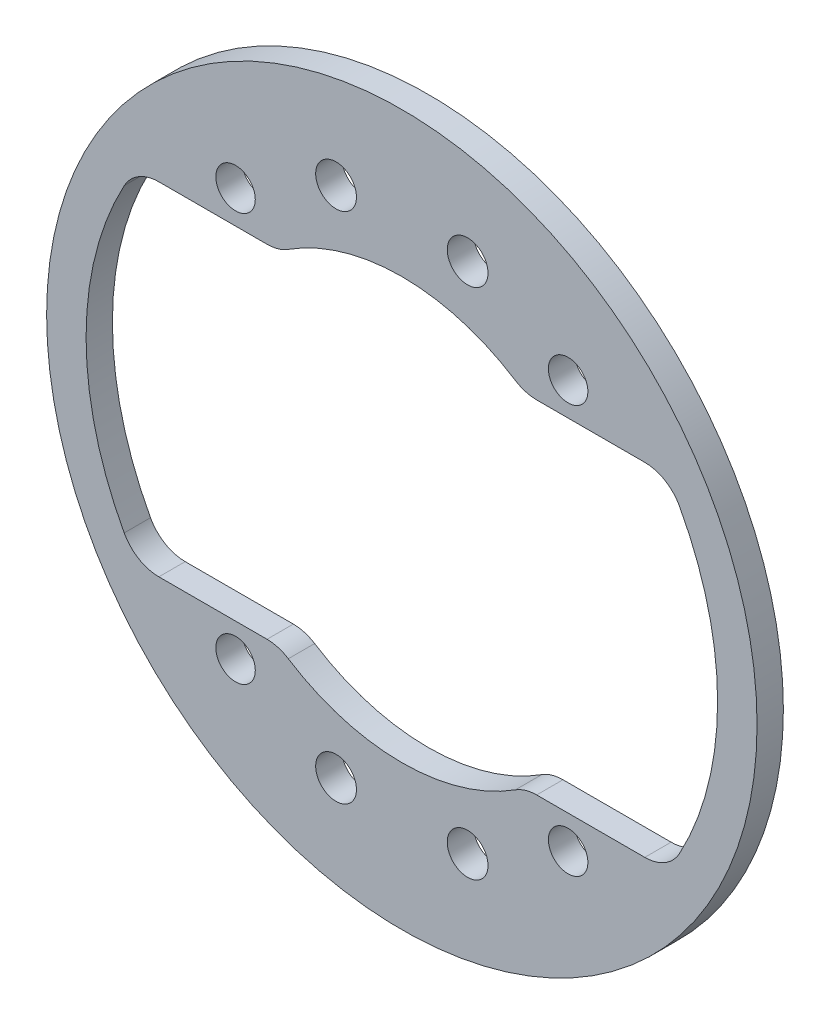
SolidWorks part; units mm, degrees
ref_plane "前视基准面" through (0, 0, 0) normal (0, 0, 1) x (1, 0, 0)
ref_plane "上视基准面" through (0, 0, 0) normal (0, 1, 0) x (1, 0, 0)
ref_plane "右视基准面" through (0, 0, 0) normal (1, 0, 0) x (0, 0, -1)
sketch "草图1" plane through (0, 0, 0) normal (0, 0, 1) x (1, 0, 0)
  line L0 (-20.1742, 13) -> (-9.3274, 13)
  line L1 (12.6392, -15.5) -> (-12.6392, -15.5) construction
  line L2 (12.6392, -15.5) -> (12.6392, 15.5) construction
  line L3 (12.6392, 15.5) -> (-12.6392, 15.5) construction
  line L4 (-12.6392, -15.5) -> (-12.6392, 15.5) construction
  line L5 (12.6392, -15.5) -> (-12.6392, 15.5) construction
  line L6 (12.6392, 15.5) -> (-12.6392, -15.5) construction
  line L7 (-20.1742, -13) -> (-9.3274, -13)
  line L8 (9.3274, 13) -> (20.1742, 13)
  line L9 (9.3274, -13) -> (20.1742, -13)
  circle A0 centre (0, 0) radius 24 construction
  circle A1 centre (-12.6392, 15.5) radius 4 construction
  circle A2 centre (-12.6392, 15.5) radius 1.5
  circle A3 centre (12.6392, 15.5) radius 1.5
  circle A4 centre (-12.6392, -15.5) radius 1.5
  circle A5 centre (12.6392, -15.5) radius 1.5
  arc A6 (9.3274, 13) -> (-9.3274, 13) centre (0, 0) ccw
  arc A7 (-9.3274, -13) -> (9.3274, -13) centre (0, 0) ccw
  circle A8 centre (0, 0) radius 27
  arc A9 (-20.1742, 13) -> (-20.1742, -13) centre (0, 0) ccw
  arc A10 (20.1742, 13) -> (20.1742, -13) centre (0, 0) cw
  point P0 (0, 0)
  dimension "D2" = 8
  dimension "D3" = 48
  dimension "D4" = 3
  dimension "D5" = 32
  dimension "D6" = 2.5
  dimension "D7" = 3
  dimension "D1" = 31
extrude "凸台-拉伸1" add sketch "草图1" along normal mid plane 2
fillet "圆角1" radius 3 8 edges at (9.3274, -13, 0) (-9.3274, -13, 0) (-9.3274, 13, 0) (9.3274, 13, 0) (20.1742, 13, 0) (20.1742, -13, 0) (-20.1742, -13, 0) (-20.1742, 13, 0)
sketch "草图2" plane through (0, 0, 1) normal (0, 0, 1) x (1, 0, 0)
  line L1 (5, -19.5) -> (-5, -19.5) construction
  line L2 (5, -19.5) -> (5, 19.5) construction
  line L3 (5, 19.5) -> (-5, 19.5) construction
  line L4 (-5, -19.5) -> (-5, 19.5) construction
  line L5 (5, -19.5) -> (-5, 19.5) construction
  line L6 (5, 19.5) -> (-5, -19.5) construction
  circle A0 centre (-5, 19.5) radius 1.55
  circle A1 centre (5, 19.5) radius 1.55
  circle A2 centre (-5, -19.5) radius 1.55
  circle A3 centre (5, -19.5) radius 1.55
  point P6 (0, 0)
  dimension "D1" = 3.1
  dimension "D2" = 10
  dimension "D3" = 39
extrude "切除-拉伸1" cut sketch "草图2" against normal through all
sketch "草图3" [suppressed] plane through (0, 0, -1) normal (0, 0, -1) x (-1, 0, 0)
  line L0 (-23.4734, 5) -> (-19.3649, 5) construction
  line L1 (-20.8567, 5.2) -> (-23.4299, 5.2)
  line L2 (-18.4662, 13) -> (-10.247, 13) construction
  line L3 (-18.4662, 13) -> (-15.4609, 13)
  circle A0 centre (-20.8567, 7) radius 2 construction
  circle A1 centre (0, 0) radius 20 construction
  arc A2 (-21.1042, 11.4286) -> (-21.1042, -11.4286) centre (0, 0) ccw construction
  circle A3 centre (-19.2445, 10.6607) radius 2 construction
  circle A4 centre (-20.8567, 7) radius 1
  circle A5 centre (-19.2445, 10.6607) radius 1
  arc A6 (-20.8567, 5.2) -> (-19.1502, 6.4273) centre (-20.8567, 7) ccw
  circle A7 centre (-19.2445, 10.6607) radius 1.8 construction
  arc A8 (-19.1502, 6.4273) -> (-15.4609, 13) centre (0, 0) cw
  arc A9 (-18.4662, 13) -> (-21.1042, 11.4286) centre (-18.4662, 10) ccw construction
  arc A10 (-18.4662, 13) -> (-21.1042, 11.4286) centre (-18.4662, 10) ccw
  arc A11 (-21.1042, 11.4286) -> (-23.4299, 5.2) centre (0, 0) ccw
  dimension "D1" = 40
  dimension "D3" = 4
  dimension "D4" = 2
  dimension "D5" = 3.6
  dimension "D2" = 5
extrude "凸台-拉伸2" [suppressed] add sketch "草图3" against normal blind 2
mirror "镜向1" [suppressed] about plane through (0, 0, 0) normal (1, 0, 0)
mirror "镜向2" [suppressed] about plane through (0, 0, 0) normal (0, 1, 0)
fillet "圆角2" [suppressed] radius 0.6
